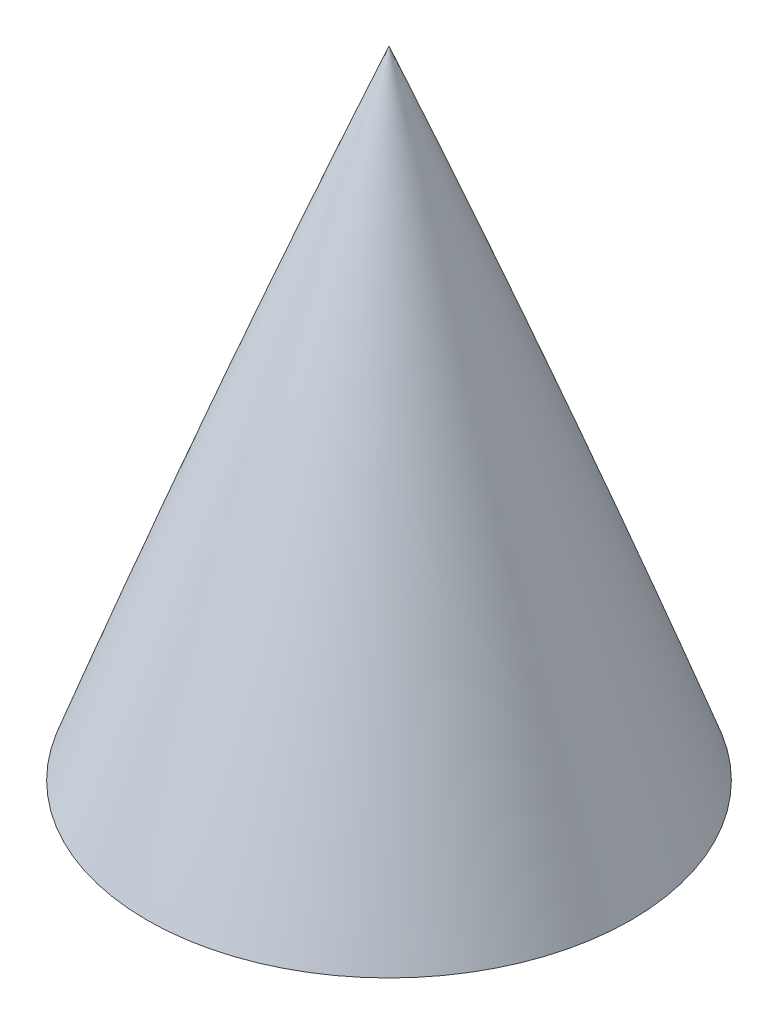
SolidWorks part; units mm, degrees
material "PVB"
ref_plane "Front Plane" through (0, 0, 0) normal (0, 0, 1) x (1, 0, 0)
ref_plane "Top Plane" through (0, 0, 0) normal (0, 1, 0) x (1, 0, 0)
ref_plane "Right Plane" through (0, 0, 0) normal (1, 0, 0) x (0, 0, -1)
sketch "Sketch2" plane through (0, 0, 0) normal (0, 0, 1) x (1, 0, 0)
  line L0 (0, 0) -> (0, 330.2) construction
  line L1 (-76.2, 0) -> (-69.85, 0)
  line L2 (0, 330.2) -> (0, 325.12)
  line L3 (0, 325.12) -> (0, 0)
  line L4 (0, 0) -> (-69.85, 0)
  arc A0 (0, 330.2) -> (-76.2, 0) centre (1014.3906, -77.7824) ccw
  dimension "D1" = 330.2
  dimension "D2" = 5.08
  dimension "D3" = 76.2
  dimension "D4" = 6.35
revolve "Revolve1" add sketch "Sketch2" angle 360 about L2
sketch "Sketch3" plane through (0, 0, 0) normal (0, -1, 0) x (1, 0, 0)
  circle A0 centre (0, 0) radius 88.9
  circle A1 centre (0, 0) radius 86.995
  dimension "D1" = 177.8
extrude "Boss-Extrude1" [suppressed] add sketch "Sketch3" along normal blind 35.56
sketch "Sketch7" plane through (0, 0, 0) normal (0, -1, 0) x (1, 0, 0)
  circle A0 centre (-188.315, 83.0177) radius 421.4958
extrude "Cut-Extrude2" cut sketch "Sketch7" against normal blind 292.1
sketch "Sketch8" plane through (0, 292.1, 0) normal (0, -1, 0) x (-1, 0, 0)
  circle A0 centre (0, 0) radius 2.413
  dimension "D1" = 4.826
extrude "Cut-Extrude3" cut sketch "Sketch8" against normal blind 12.7
